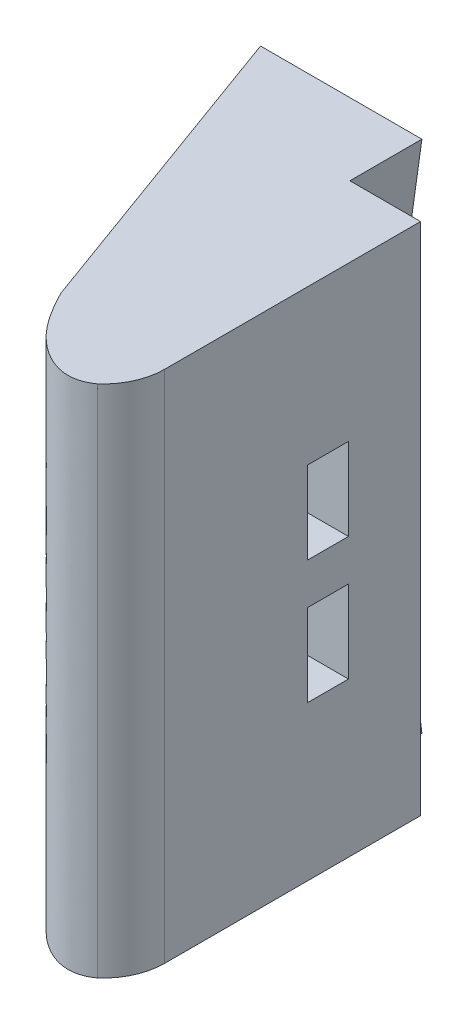
SolidWorks part; units mm, degrees
ref_plane "Front Plane" through (0, 0, 0) normal (0, 0, 1) x (1, 0, 0)
ref_plane "Top Plane" through (0, 0, 0) normal (0, 1, 0) x (1, 0, 0)
ref_plane "Right Plane" through (0, 0, 0) normal (1, 0, 0) x (0, 0, -1)
sketch "Sketch1" plane through (0, 0, 0) normal (0, 1, 0) x (1, 0, 0)
  line L0 (0, 0) -> (20, 0)
  line L1 (20, 0) -> (20, -24.8557)
  line L2 (0, 0) -> (8.5505, -23.4923)
  arc A0 (20, -24.8557) -> (17.9736, -29.3468) centre (14.01, -24.8557) cw
  spline S0 degree 3 poles (17.9736, -29.3468) (16.2811, -30.6017) (11.8764, -29.3199) (9.5982, -25.5616) (8.5505, -23.4923) knots 0 0 0 0 0.430743 1 1 1 1
  point P8 (20, -30)
  dimension "D5" = 5.99
  dimension "D6" = 25
  dimension "D1" = 30
  dimension "D3" = 20
  dimension "D4" = 70
extrude "Boss-Extrude1" add sketch "Sketch1" along normal blind 50
sketch "Sketch2" plane through (0, 0, 0) normal (0, 0, -1) x (-1, 0, 0)
  line L0 (-20, 25) -> (0, 25) construction
  line L1 (-20, 50) -> (-20, 0) construction
  line L2 (0, 50) -> (0, 0) construction
  circle A0 centre (-14, 31) radius 1.6
  circle A1 centre (-14, 19) radius 1.6
  dimension "D1" = 3.2
  dimension "D2" = 6
  dimension "D3" = 6
extrude "Cut-Extrude1" cut sketch "Sketch2" against normal blind 20
sketch "Sketch4" plane through (20, 0, 0) normal (1, 0, 0) x (0, 0, -1)
  line L0 (0, 25) -> (-24.8557, 25) construction
  line L1 (0, 50) -> (0, 0) construction
  line L2 (-24.8557, 50) -> (-24.8557, 0) construction
  line L3 (-7, 15) -> (-11, 15)
  line L4 (-7, 27) -> (-11, 27)
  line L5 (-7, 27) -> (-7, 35)
  line L6 (-7, 35) -> (-11, 35)
  line L7 (-11, 27) -> (-11, 35)
  line L8 (-11, 23) -> (-11, 15)
  line L9 (-7, 23) -> (-11, 23)
  line L10 (-7, 23) -> (-7, 15)
  point P10 (-7, 31)
  point P11 (-9, 27)
  dimension "D1" = 6
  dimension "D2" = 9
  dimension "D3" = 8
  dimension "D4" = 4
extrude "Cut-Extrude2" cut sketch "Sketch4" against normal blind 12
sketch "Sketch5" plane through (0, 0, 0) normal (0, 0, -1) x (-1, 0, 0)
  line L0 (-20, 25) -> (0, 25) construction
  line L1 (-20, 50) -> (-20, 0) construction
  line L2 (0, 50) -> (0, 0) construction
  line L3 (-14, 31) -> (-20, 73.6922) construction
  line L4 (-14, 31) -> (-14.835, 36.9416) construction
  line L5 (-14.835, 36.9416) -> (-11.3691, 37.4287) construction
  line L6 (-11.3691, 37.4287) -> (-12.7608, 47.3314)
  line L14 (-12.7608, 47.3314) -> (-13.1359, 50)
  line L15 (0, 50) -> (-20, 50) construction
  line L16 (-13.1359, 50) -> (0, 50)
  line L17 (0, 50) -> (0, 37.4287)
  line L18 (0, 37.4287) -> (-11.3691, 37.4287)
  line L19 (0, 12.5713) -> (-11.3691, 12.5713)
  line L20 (0, 0) -> (0, 12.5713)
  line L21 (-13.1359, 0) -> (0, 0)
  line L22 (-12.7608, 2.6686) -> (-13.1359, 0)
  line L23 (-11.3691, 12.5713) -> (-12.7608, 2.6686)
  dimension "D1" = 8
  dimension "D2" = 6
  dimension "D3" = 90
  dimension "D4" = 3.5
  dimension "D5" = 90
  dimension "D6" = 10
  dimension "D7" = 180
extrude "Boss-Extrude4" add sketch "Sketch5" along normal blind 7
sketch "Sketch7" plane through (0, 50, 0) normal (0, 1, 0) x (1, 0, 0)
  line L0 (0, 0) -> (0, 7)
  line L1 (0, 7) -> (-2.5478, 7)
  line L2 (-2.5478, 7) -> (0, 0)
  dimension "D1" = 20
extrude "Boss-Extrude12" add sketch "Sketch7" against normal blind 12.57
sketch "Sketch8" plane through (0, 0, 0) normal (0, -1, 0) x (-1, 0, 0)
  line L0 (0, 0) -> (2.5478, 7)
  line L1 (2.5478, 7) -> (0, 7)
  line L2 (0, 7) -> (0, 0)
extrude "Boss-Extrude13" add sketch "Sketch8" against normal blind 12.57
